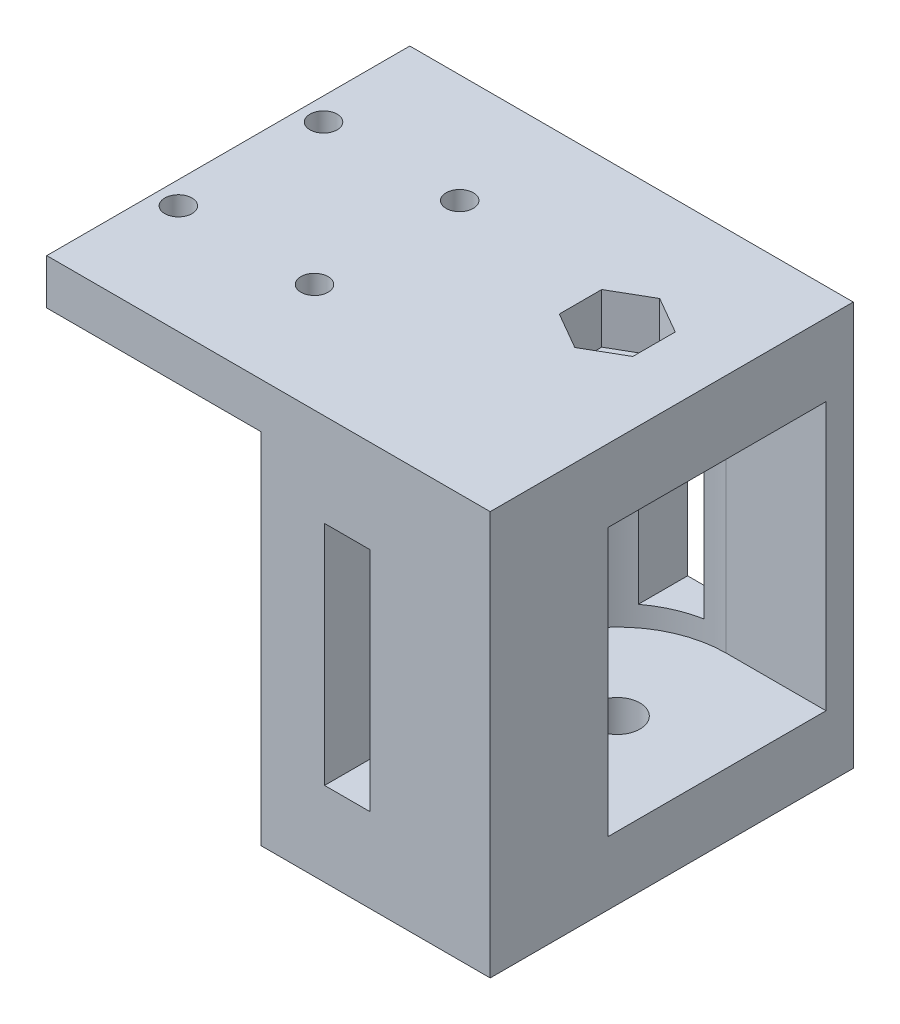
SolidWorks part; units mm, degrees
ref_plane "Front" through (0, 0, 0) normal (0, 0, 1) x (1, 0, 0)
ref_plane "Top" through (0, 0, 0) normal (0, 1, 0) x (1, 0, 0)
ref_plane "Right" through (0, 0, 0) normal (1, 0, 0) x (0, 0, -1)
sketch "Sketch1" plane through (0, 0, 0) normal (0, 0, 1) x (1, 0, 0)
  line L0 (48.86, -22.25) -> (0, -22.25)
  line L1 (48.86, -22.25) -> (48.86, 22.25)
  line L2 (0, -22.25) -> (0, 22.25)
  line L3 (48.86, 22.25) -> (0, 22.25)
  line L4 (48.86, -22.25) -> (0, 22.25) construction
  line L5 (0, -22.25) -> (48.86, 22.25) construction
  line L6 (26.86, -15.25) -> (48.86, -15.25) construction
  line L7 (26.86, -15.25) -> (26.86, 14.25) construction
  line L8 (48.86, -15.25) -> (48.86, 14.25) construction
  line L9 (26.86, 14.25) -> (48.86, 14.25) construction
  line L10 (26.86, -15.25) -> (48.86, 14.25) construction
  line L11 (48.86, -15.25) -> (26.86, 14.25) construction
  line L12 (37.86, -0.5) -> (37.86, 22.25) construction
  line L13 (30.61, -13) -> (35.61, -13)
  line L14 (30.61, -13) -> (30.61, 12)
  line L15 (35.61, -13) -> (35.61, 12)
  line L16 (30.61, 12) -> (35.61, 12)
  line L17 (30.61, -13) -> (35.61, 12) construction
  line L18 (35.61, -13) -> (30.61, 12) construction
  line L19 (23.61, -22.25) -> (23.61, 17.25)
  line L20 (23.61, -13) -> (23.61, 12) construction
  line L22 (23.61, 17.25) -> (0, 17.25)
  point P1 (24.43, 0)
  point P2 (37.86, -0.5)
  point P8 (0, 0)
  point P13 (0, 0)
  point P15 (33.11, -0.5)
  point P23 (0, 17.25)
  dimension "D1" = 29.5
  dimension "D2" = 8
  dimension "D3" = 7
  dimension "D4" = 37.86
  dimension "D5" = 11
  dimension "D6" = 25
  dimension "D7" = 4.75
  dimension "D8" = 5
  dimension "D10" = 5
  dimension "D9" = 7
extrude "Boss-Extrude1" add sketch "Sketch1" along normal blind 25 and the other way blind 15 contours L22 L19 L0 L1 L3 L2 L14 L16 L15 L13
sketch "Sketch2" plane through (0, 0, 0) normal (0, 1, 0) x (1, 0, 0)
  line L0 (37.86, 12) -> (48.86, 12)
  line L1 (48.86, -25) -> (48.86, 15) construction
  line L2 (37.86, -12) -> (48.86, -12)
  line L3 (48.86, 12) -> (48.86, -12)
  arc A0 (37.86, 12) -> (37.86, -12) centre (37.86, 0) ccw
  dimension "D1" = 24
extrude "Cut-Extrude1" cut sketch "Sketch2" against normal up to vertex and the other way up to vertex
sketch "Sketch5" plane through (0, -15.25, 0) normal (0, 1, 0) x (1, 0, 0)
  line L0 (26.86, 0) -> (48.86, 0) construction
  circle A0 centre (37.86, 0) radius 2.5
  dimension "D1" = 5
extrude "Cut-Extrude4" cut sketch "Sketch5" against normal through all both and the other way through all
sketch "Sketch6" plane through (0, 22.25, 0) normal (0, 1, 0) x (1, 0, 0)
  line L0 (48.86, -25) -> (48.86, 15) construction
  line L1 (41.91, 2.3383) -> (37.86, 4.6765)
  line L2 (37.86, 4.6765) -> (33.81, 2.3383)
  line L3 (33.81, 2.3383) -> (33.81, -2.3383)
  line L4 (33.81, -2.3383) -> (37.86, -4.6765)
  line L5 (37.86, -4.6765) -> (41.91, -2.3383)
  line L6 (41.91, -2.3383) -> (41.91, 2.3383)
  circle A0 centre (37.86, 0) radius 4.05 construction
  dimension "D1" = 8.1
extrude "Cut-Extrude5" cut sketch "Sketch6" against normal blind 5.5
sketch "Sketch7" plane through (0, 22.25, 0) normal (0, 1, 0) x (1, 0, 0)
  line L0 (10, 15) -> (10, -25) construction
  line L3 (2.5, 3) -> (2.5, -13) construction
  line L4 (2.5, 3) -> (17.5, 3) construction
  line L5 (2.5, -13) -> (17.5, -13) construction
  line L6 (17.5, 3) -> (17.5, -13) construction
  line L7 (2.5, 3) -> (17.5, -13) construction
  line L8 (2.5, -13) -> (17.5, 3) construction
  line L10 (0, 15) -> (0, -25) construction
  line L11 (48.86, 15) -> (0, 15) construction
  line L12 (48.86, -25) -> (0, -25) construction
  circle A0 centre (2.5, 3) radius 1.5
  circle A1 centre (17.5, 3) radius 1.5
  circle A2 centre (17.5, -13) radius 1.5
  circle A3 centre (2.5, -13) radius 1.5
  point P2 (10, 11.0312)
  point P3 (10, 15)
  point P4 (10, -25)
  point P7 (10, -5)
  point P17 (10, 3)
  point P18 (0, 0)
  point P21 (0, 0)
  dimension "D1" = 3
  dimension "D4" = 2.5
  dimension "D2" = 16
  dimension "D3" = 15
extrude "Cut-Extrude6" cut sketch "Sketch7" against normal through all
